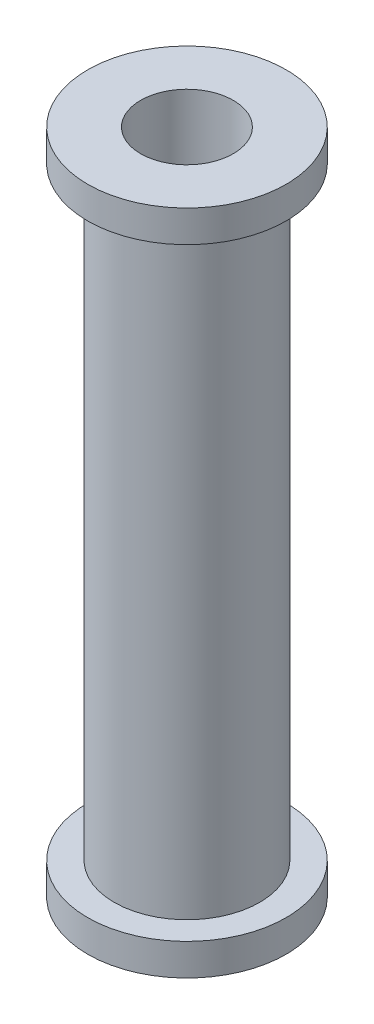
SolidWorks part; units mm, degrees
ref_plane "Front Plane" through (0, 0, 0) normal (0, 0, 1) x (1, 0, 0)
ref_plane "Top Plane" through (0, 0, 0) normal (0, 1, 0) x (1, 0, 0)
ref_plane "Right Plane" through (0, 0, 0) normal (1, 0, 0) x (0, 0, -1)
sketch "Sketch1" plane through (0, 0, 0) normal (0, 1, 0) x (1, 0, 0)
  circle A0 centre (0, 0) radius 9.525
  circle A1 centre (0, 0) radius 4.445
  dimension "D1" = 19.05
  dimension "D2" = 8.89
extrude "Boss-Extrude1" add sketch "Sketch1" along normal blind 3.048
sketch "Sketch2" plane through (0, 3.048, 0) normal (0, 1, 0) x (1, 0, 0)
  circle A0 centre (0, 0) radius 6.985
  circle A1 centre (0, 0) radius 4.445
  circle A2 centre (0, 0) radius 4.445 construction
  dimension "D1" = 13.97
extrude "Boss-Extrude2" add sketch "Sketch2" along normal blind 57.912
sketch "Sketch3" plane through (0, 60.96, 0) normal (0, 1, 0) x (1, 0, 0)
  circle A1 centre (0, 0) radius 9.525
  circle A2 centre (0, 0) radius 6.985
  circle A3 centre (0, 0) radius 4.445
  circle A4 centre (0, 0) radius 9.525 construction
  circle A5 centre (0, 0) radius 6.985 construction
  circle A6 centre (0, 0) radius 4.445 construction
  circle M1 centre (0, 0) radius 6.985
  circle M2 centre (0, 0) radius 4.445
extrude "Boss-Extrude3" add sketch "Sketch3" along normal blind 3.048 contours A1 M1 | M1 M2
